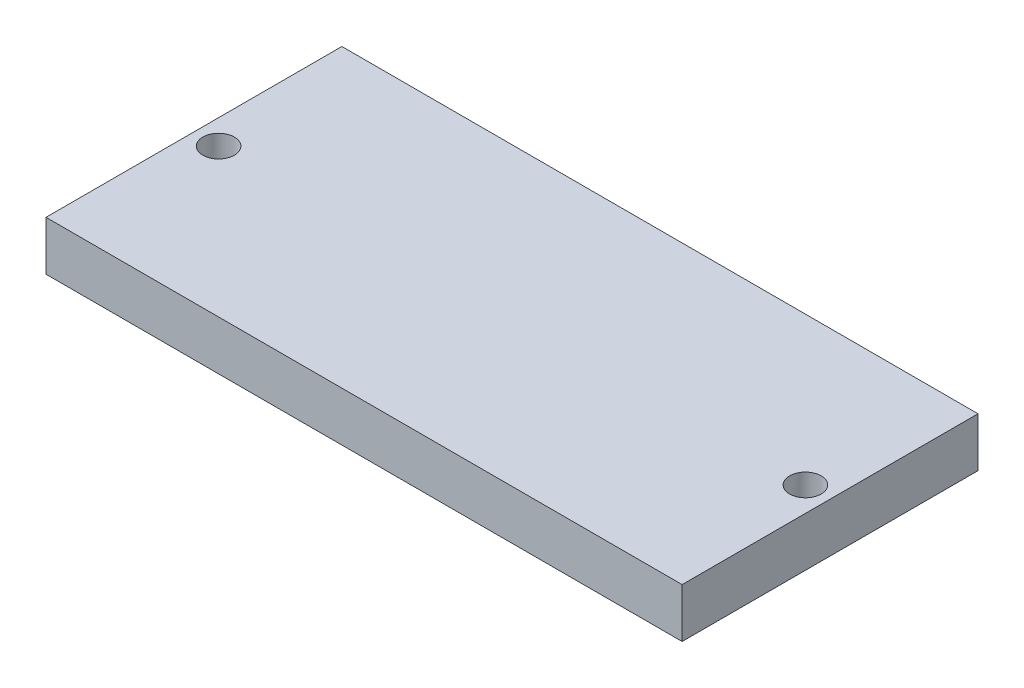
SolidWorks part; units mm, degrees
ref_plane "Alzado" through (0, 0, 0) normal (0, 0, 1) x (1, 0, 0)
ref_plane "Planta" through (0, 0, 0) normal (0, 1, 0) x (1, 0, 0)
ref_plane "Vista lateral" through (0, 0, 0) normal (1, 0, 0) x (0, 0, -1)
sketch "Croquis1" plane through (0, 0, 0) normal (0, 1, 0) x (1, 0, 0)
  line L1 (-32.25, -15) -> (32.25, -15)
  line L2 (-32.25, -15) -> (-32.25, 15)
  line L3 (-32.25, 15) -> (32.25, 15)
  line L4 (32.25, -15) -> (32.25, 15)
  line L5 (-32.25, -15) -> (32.25, 15) construction
  line L6 (-32.25, 15) -> (32.25, -15) construction
  point P0 (0, 0)
  dimension "D1" = 64.5
  dimension "D2" = 30
extrude "Saliente-Extruir1" add sketch "Croquis1" along normal blind 5
sketch "Croquis2" plane through (0, 5, 0) normal (0, 1, 0) x (1, 0, 0)
  line L0 (-29.75, 15) -> (-29.75, -15) construction
  line L1 (32.25, 15) -> (-32.25, 15) construction
  line L2 (-32.25, -15) -> (32.25, -15) construction
  line L3 (29.75, 15) -> (29.75, -15) construction
  line L4 (-32.25, 15) -> (-32.25, -15) construction
  line L5 (32.25, -15) -> (32.25, 15) construction
  line L6 (-32.25, 0) -> (32.25, 0) construction
  circle A0 centre (-29.75, 0) radius 1.6
  circle A1 centre (29.75, 0) radius 1.6
  dimension "D3" = 3.2
  dimension "D4" = 3.2
  dimension "D1" = 2.5
  dimension "D2" = 2.5
extrude "Cortar-Extruir1" cut sketch "Croquis2" against normal through all
